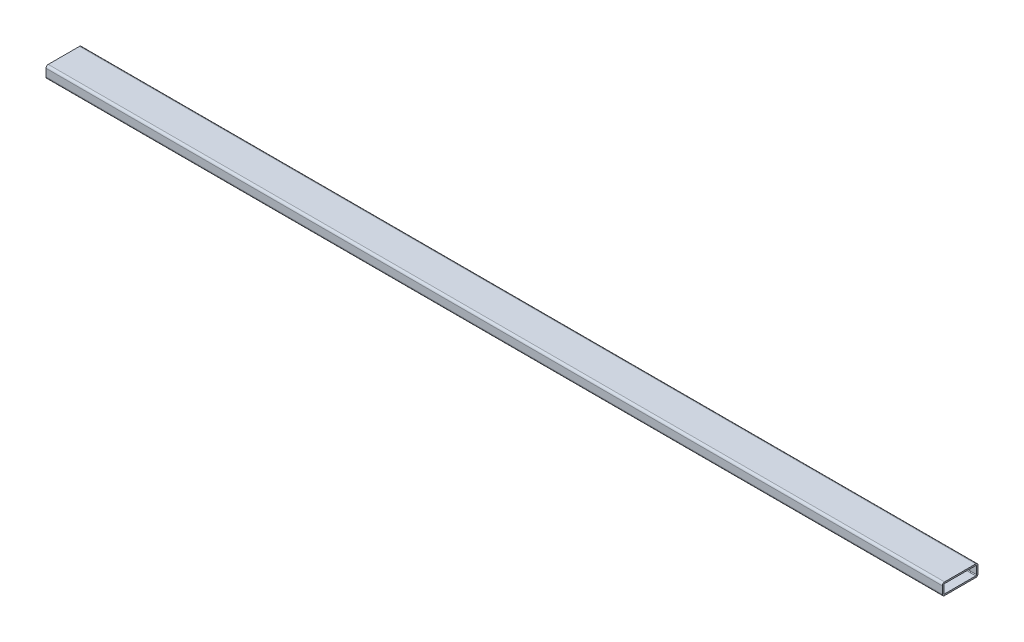
SolidWorks part; units mm, degrees
ref_plane "Front Plane" through (0, 0, 0) normal (0, 0, 1) x (1, 0, 0)
ref_plane "Top Plane" through (0, 0, 0) normal (0, 1, 0) x (1, 0, 0)
ref_plane "Right Plane" through (0, 0, 0) normal (1, 0, 0) x (0, 0, -1)
sketch "Sketch1" plane through (0, 0, 0) normal (1, 0, 0) x (0, 0, -1)
  line L0 (33.3248, 22.225) -> (-33.3248, 22.225)
  line L1 (33.3248, 25.4) -> (-33.3248, 25.4)
  line L2 (38.1, 20.6248) -> (38.1, 4.7752)
  line L3 (33.3248, 0) -> (-33.3248, 0)
  line L4 (-38.1, 20.6248) -> (-38.1, 4.7752)
  line L5 (-34.925, 20.6248) -> (-34.925, 4.7752)
  line L6 (33.3248, 3.175) -> (-33.3248, 3.175)
  line L7 (34.925, 20.6248) -> (34.925, 4.7752)
  arc A0 (38.1, 20.6248) -> (33.3248, 25.4) centre (33.3248, 20.6248) ccw
  arc A1 (38.1, 4.7752) -> (33.3248, 0) centre (33.3248, 4.7752) cw
  arc A2 (-33.3248, 0) -> (-38.1, 4.7752) centre (-33.3248, 4.7752) cw
  arc A3 (-38.1, 20.6248) -> (-33.3248, 25.4) centre (-33.3248, 20.6248) cw
  arc A4 (-34.925, 20.6248) -> (-33.3248, 22.225) centre (-33.3248, 20.6248) cw
  arc A5 (-33.3248, 3.175) -> (-34.925, 4.7752) centre (-33.3248, 4.7752) cw
  arc A6 (34.925, 4.7752) -> (33.3248, 3.175) centre (33.3248, 4.7752) cw
  arc A7 (34.925, 20.6248) -> (33.3248, 22.225) centre (33.3248, 20.6248) ccw
  point P1 (0, 0)
  point P5 (0, 0)
  dimension "D1" = 4.7752
  dimension "D2" = 25.4
  dimension "D3" = 76.2
  dimension "D4" = 3.175
extrude "Boss-Extrude1" add sketch "Sketch1" along normal mid plane 1914.525
